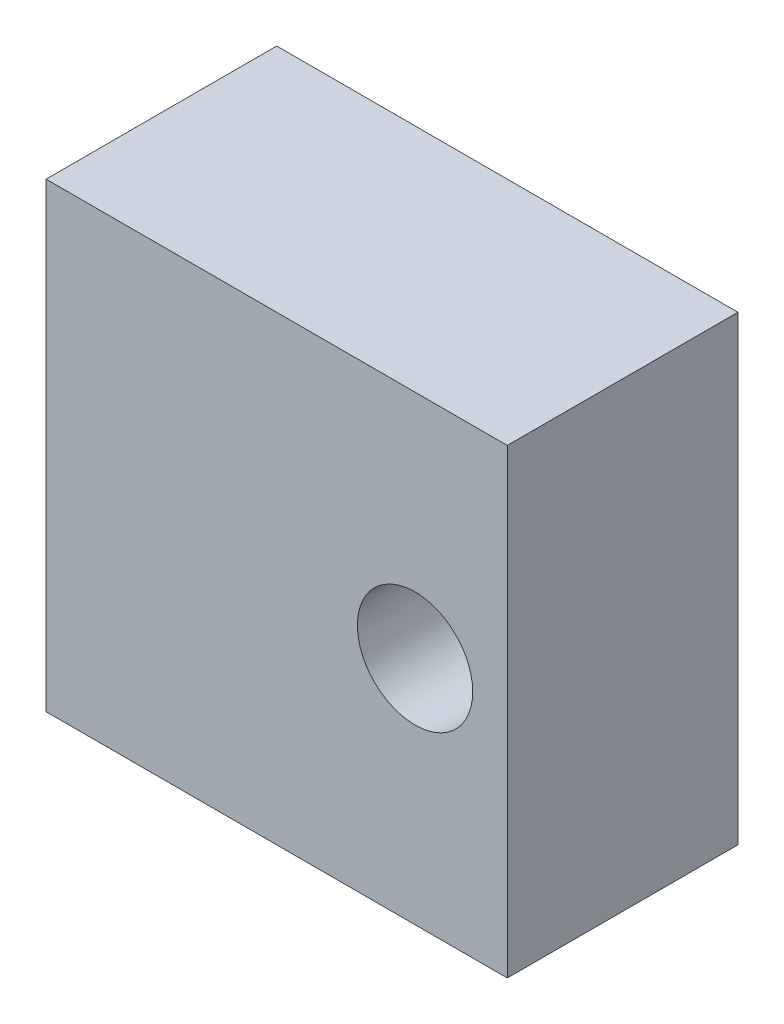
SolidWorks part; units mm, degrees
ref_plane "前视基准面" through (0, 0, 0) normal (0, 0, 1) x (1, 0, 0)
ref_plane "上视基准面" through (0, 0, 0) normal (0, 1, 0) x (1, 0, 0)
ref_plane "右视基准面" through (0, 0, 0) normal (1, 0, 0) x (0, 0, -1)
sketch "草图1" plane through (0, 0, 0) normal (0, 0, 1) x (1, 0, 0)
  line L1 (-8.6087, 6.913) -> (11.3913, 6.913)
  line L2 (-8.6087, 6.913) -> (-8.6087, -13.087)
  line L3 (-8.6087, -13.087) -> (11.3913, -13.087)
  line L4 (11.3913, 6.913) -> (11.3913, -13.087)
  dimension "D1" = 20
  dimension "D2" = 20
extrude "凸台-拉伸1" add sketch "草图1" along normal blind 10
ref_plane "基准面4" through (11.3913, 6.913, 10) normal (0, 1, 0) x (1, 0, 0)
sketch "草图4" plane through (0, 0, 10) normal (0, 0, 1) x (1, 0, 0)
  circle A0 centre (7.3913, -3.087) radius 2.5
  dimension "D3" = 5
extrude "切除-拉伸1" cut sketch "草图4" against normal blind 10
